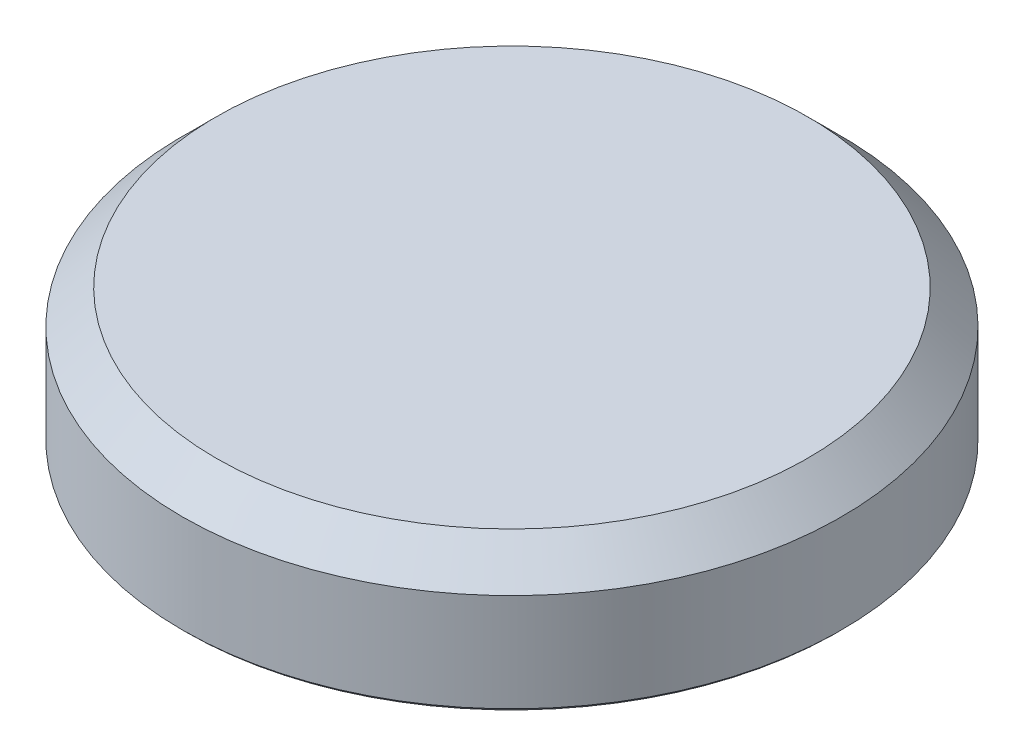
SolidWorks part; units mm, degrees
ref_plane "Front Plane" through (0, 0, 0) normal (0, 0, 1) x (1, 0, 0)
ref_plane "Top Plane" through (0, 0, 0) normal (0, 1, 0) x (1, 0, 0)
ref_plane "Right Plane" through (0, 0, 0) normal (1, 0, 0) x (0, 0, -1)
sketch "Sketch2" plane through (0, 0, 0) normal (0, 1, 0) x (1, 0, 0)
  circle A0 centre (0, 0) radius 24.765
  dimension "D1" = 49.53
extrude "Boss-Extrude1" add sketch "Sketch2" along normal blind 10.16
chamfer "Chamfer1" distance 2.54 angle 45 1 edges at (0, 10.16, 24.765)
chamfer "Chamfer2" distance 0.254 angle 45 1 edges at (0, 0, 24.765)
sketch "Sketch3" plane through (0, 0, 0) normal (0, -1, 0) x (1, 0, 0)
  line L0 (0, 0) -> (-4.9391, 4.9391) construction
  line L1 (-4.9391, 4.9391) -> (-4.9391, 0) construction
  line L2 (-4.9391, 0) -> (0, 0) construction
  line L3 (4.9391, 4.9391) -> (4.9391, 0) construction
  line L4 (4.9391, 0) -> (4.9391, -4.9391) construction
  line L5 (4.9391, -4.9391) -> (0, -4.9391) construction
  line L6 (0, -4.9391) -> (-4.9391, -4.9391) construction
  line L7 (-4.9391, -4.9391) -> (-4.9391, 0) construction
  point P0 (-4.9391, 4.9391)
  point P8 (4.9391, 4.9391)
  point P9 (4.9391, -4.9391)
  point P10 (-4.9391, -4.9391)
  point P11 (0, 0)
  dimension "D1" = 6.985
  dimension "D3" = 6.985
  dimension "D2" = 4
hole_wizard "B (0.238) Diameter Hole1" positions "Sketch4" profile "Sketch5" hole size "B" standard "ANSI Inch"
sketch "Sketch4" plane through (0, 0, 0) normal (0, -1, 0) x (-1, 0, 0)
  point P0 (-4.9391, 4.9391)
  point P3 (4.9391, 4.9391)
  point P6 (4.9391, -4.9391)
  point P9 (-4.9391, -4.9391)
sketch "Sketch5" plane through (4.9391, 0, -4.9391) normal (1, 0, 0) x (0, 0, -1)
  line L0 (0, 0) -> (0, 5.6262)
  line L1 (0, 5.6262) -> (3.0226, 3.81)
  line L2 (3.0226, 3.81) -> (3.0226, 0)
  line L5 (3.0226, 0) -> (0, 0)
  line L10 (0, 5.6262) -> (-3.0226, 3.81) construction
  line L11 (0, -6.35) -> (0, 107.95) construction
  dimension "Hole Dia." = 6.0452
  dimension "Hole Depth" = 3.81
  dimension "Drill Angle" = 118
hole_wizard "1/4 (0.25) Diameter Hole1" positions "Sketch6" profile "Sketch7" hole size "1/4" standard "ANSI Inch"
sketch "Sketch6" plane through (0, 0, 0) normal (0, -1, 0) x (-1, 0, 0)
  point P0 (0, 0)
sketch "Sketch7" plane through (0, 0, 0) normal (1, 0, 0) x (0, 0, -1)
  line L0 (0, 0) -> (0, 9.5277)
  line L1 (0, 9.5277) -> (3.175, 7.62)
  line L2 (3.175, 7.62) -> (3.175, 0)
  line L5 (3.175, 0) -> (0, 0)
  line L10 (0, 9.5277) -> (-3.175, 7.62) construction
  line L11 (0, -6.35) -> (0, 107.95) construction
  dimension "Hole Dia." = 6.35
  dimension "Hole Depth" = 7.62
  dimension "Drill Angle" = 118
